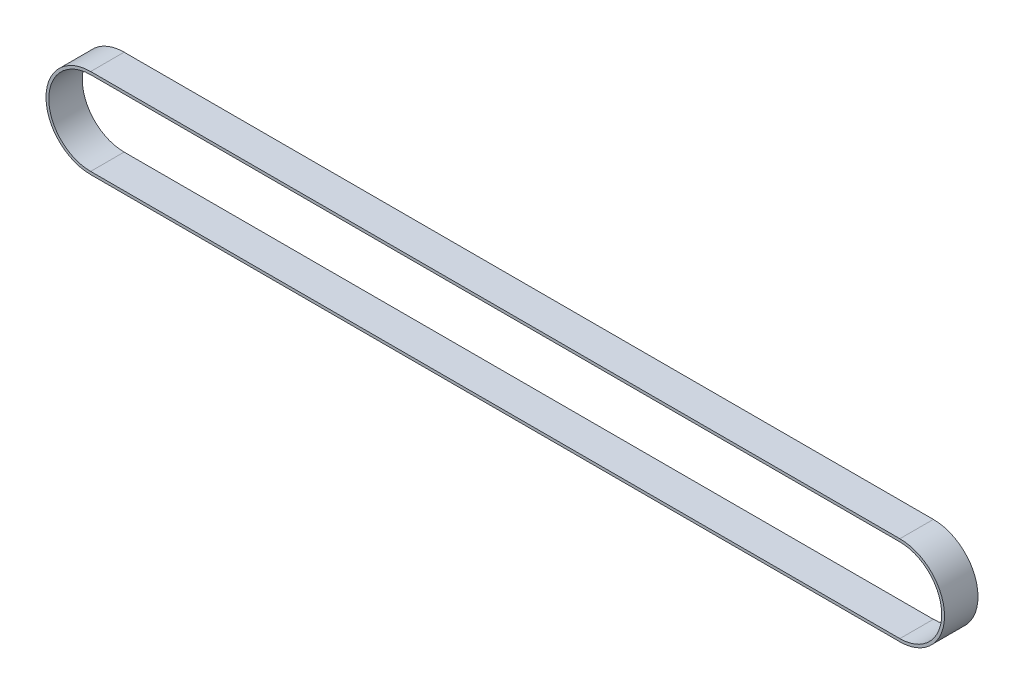
SolidWorks part; units mm, degrees
ref_plane "Front Plane" through (0, 0, 0) normal (0, 0, 1) x (1, 0, 0)
ref_plane "Top Plane" through (0, 0, 0) normal (0, 1, 0) x (1, 0, 0)
ref_plane "Right Plane" through (0, 0, 0) normal (1, 0, 0) x (0, 0, -1)
sketch "Sketch2" plane through (0, 0, 0) normal (0, 0, 1) x (1, 0, 0)
  line L0 (0, 0) -> (1, 0) construction
  line L1 (0, 0) -> (0, 1) construction
  line L2 (0, 7) -> (145, 7)
  line L3 (145, -8) -> (0, -8)
  arc A0 (0, -8) -> (0, 7) centre (0, -0.5) cw
  arc A1 (145, 7) -> (145, -8) centre (145, -0.5) cw
extrude "Extrude-Thin1" add sketch "Sketch2" against normal blind 6 from offset 0.5 thin thin type one direction wall 0.5 offset against normal yes
